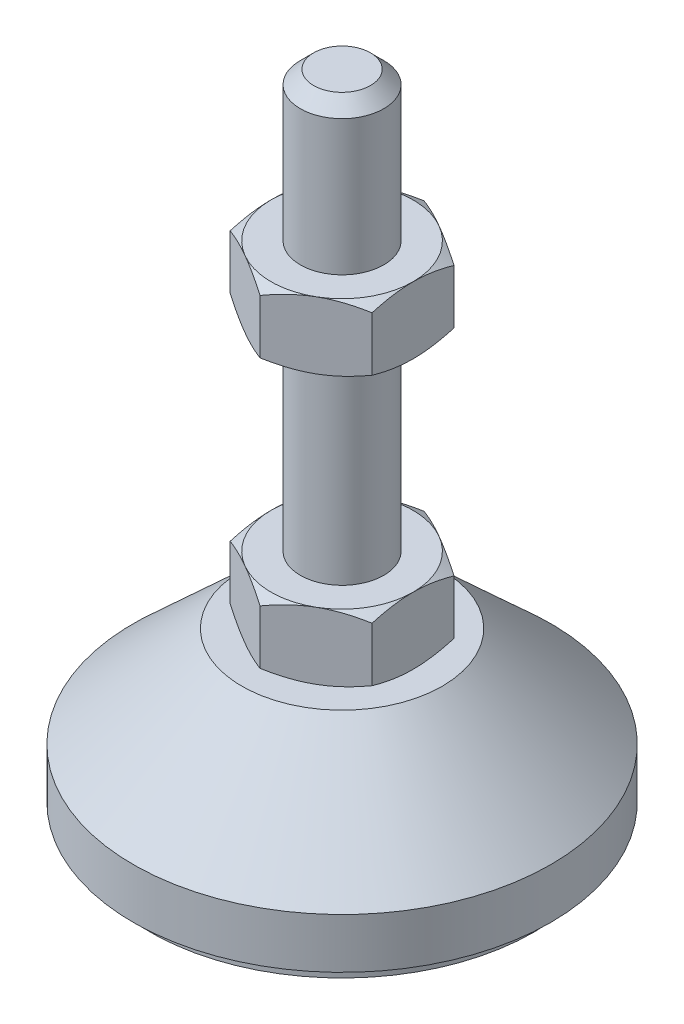
SolidWorks part; units mm, degrees
ref_plane "Спереди" through (0, 0, 0) normal (0, 0, 1) x (1, 0, 0)
ref_plane "Сверху" through (0, 0, 0) normal (0, 1, 0) x (1, 0, 0)
ref_plane "Справа" through (0, 0, 0) normal (1, 0, 0) x (0, 0, -1)
sketch "Эскиз1" plane through (0, 0, 0) normal (0, 0, 1) x (1, 0, 0)
  line L0 (0, 0) -> (-23, 0)
  line L1 (-23, 0) -> (-23, 2)
  line L2 (-23, 2) -> (-25, 2)
  line L3 (-25, 2) -> (-25, 8)
  line L4 (-25, 8) -> (-12, 20)
  line L5 (-12, 20) -> (-5, 20)
  line L12 (-5, 28) -> (-5, 76.4)
  line L13 (-5, 76.4) -> (-3.4, 78)
  line L14 (-3.4, 78) -> (0, 78)
  line L15 (0, 78) -> (0, 0) construction
  line L16 (-5, 20) -> (0, 20) construction
  line L17 (0, 0) -> (0, 78)
  line L18 (0, 0) -> (0, -7.9595) construction
  line L19 (-5, 28) -> (-5, 20)
  point P8 (-5, 52.2)
  point P23 (-8.5, 20)
  dimension "D1" = 10
  dimension "D2" = 20
  dimension "D3" = 8
  dimension "D4" = 50
  dimension "D5" = 5
  dimension "D6" = 1.6
  dimension "D7" = 45
  dimension "D8" = 24
  dimension "D9" = 2
  dimension "D10" = 50
  dimension "D11" = 6
revolve "Повернуть1" add sketch "Эскиз1" angle 360 about L17
sketch "Эскиз2" plane through (0, 20, 0) normal (0, 1, 0) x (1, 0, 0)
  line L1 (0, 9.815) -> (-8.5, 4.9075)
  line L2 (-8.5, 4.9075) -> (-8.5, -4.9075)
  line L3 (-8.5, -4.9075) -> (0, -9.815)
  line L4 (0, -9.815) -> (8.5, -4.9075)
  line L5 (8.5, -4.9075) -> (8.5, 4.9075)
  line L6 (8.5, 4.9075) -> (0, 9.815)
  circle A0 centre (0, 0) radius 8.5 construction
  dimension "D1" = 17
extrude "Бобышка-Вытянуть1" add sketch "Эскиз2" along normal up to vertex (8 mm away) up to point (-5, 28, 0)
ref_plane "Плоскость1" through (0, 52.2, 0) normal (0, 1, 0) x (1, 0, 0)
sketch "Эскиз3" plane through (0, 52.2, 0) normal (0, 1, 0) x (1, 0, 0)
  line L6 (8.5, 4.9075) -> (0, 9.815)
  line L7 (0, 9.815) -> (-8.5, 4.9075)
  line L8 (-8.5, 4.9075) -> (-8.5, -4.9075)
  line L9 (-8.5, -4.9075) -> (0, -9.815)
  line L10 (0, -9.815) -> (8.5, -4.9075)
  line L11 (8.5, -4.9075) -> (8.5, 4.9075)
  line L12 (8.5, 4.9075) -> (0, 9.815)
  line L13 (0, 9.815) -> (-8.5, 4.9075)
  line L14 (-8.5, 4.9075) -> (-8.5, -4.9075)
  line L15 (-8.5, -4.9075) -> (0, -9.815)
  line L16 (0, -9.815) -> (8.5, -4.9075)
  line L17 (8.5, -4.9075) -> (8.5, 4.9075)
  dimension "D1" = 0
extrude "Бобышка-Вытянуть2" add sketch "Эскиз3" along normal blind 8
sketch "Эскиз4" plane through (0, 0, 0) normal (0, 0, 1) x (1, 0, 0)
  line L0 (-8.5, 60.2) -> (-15.4282, 56.2)
  line L1 (-15.4282, 56.2) -> (-15.4282, 60.2)
  line L2 (-15.4282, 60.2) -> (-8.5, 60.2)
  line L3 (-15.4282, 56.2) -> (-8.5, 52.2)
  line L4 (50, 52.2) -> (-50, 52.2) construction
  line L5 (-8.5, 52.2) -> (-15.4282, 52.2)
  line L6 (-15.4282, 52.2) -> (-15.4282, 56.2)
  line L7 (-8.5, 60.2) -> (-8.5, 52.2) construction
  line L8 (-8.5, 28) -> (-15.4282, 28)
  line L9 (-15.4282, 28) -> (-15.4282, 24)
  line L10 (-15.4282, 24) -> (-8.5, 28)
  line L11 (-8.5, 20) -> (-15.4282, 24)
  line L12 (-15.4282, 24) -> (-15.4282, 20)
  line L13 (-15.4282, 20) -> (-8.5, 20)
  line L14 (0, 78) -> (0, 96.3793) construction
  dimension "D1" = 30
  dimension "D2" = 30
revolve "Вырез-Повернуть2" cut sketch "Эскиз4" angle 360 about L14
